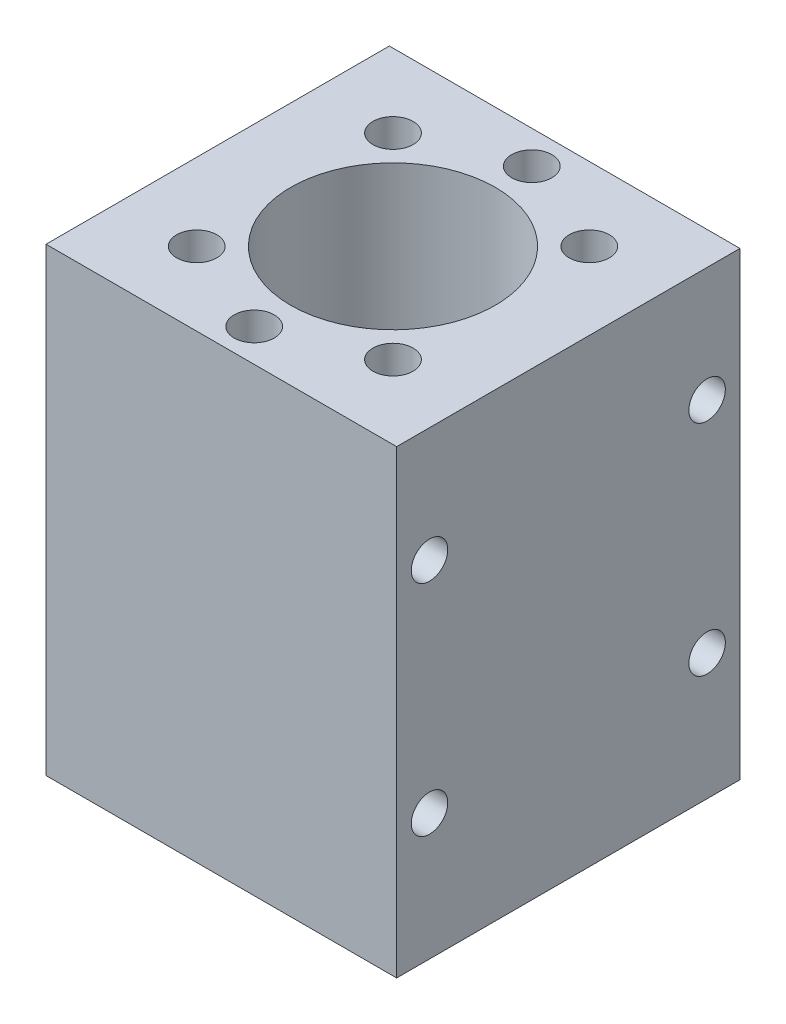
SolidWorks part; units mm, degrees
ref_plane "Спереди" through (0, 0, 0) normal (0, 0, 1) x (1, 0, 0)
ref_plane "Сверху" through (0, 0, 0) normal (0, 1, 0) x (1, 0, 0)
ref_plane "Справа" through (0, 0, 0) normal (1, 0, 0) x (0, 0, -1)
sketch "Эскиз1" plane through (0, 0, 0) normal (0, 1, 0) x (1, 0, 0)
  line L1 (-24, -23.5) -> (24, -23.5)
  line L2 (-24, -23.5) -> (-24, 23.5)
  line L3 (-24, 23.5) -> (24, 23.5)
  line L4 (24, -23.5) -> (24, 23.5)
  line L5 (-24, -23.5) -> (24, 23.5) construction
  line L6 (-24, 23.5) -> (24, -23.5) construction
  circle A0 centre (0, 0) radius 14
  dimension "D1" = 28
extrude "Бобышка-Вытянуть1" add sketch "Эскиз1" along normal blind 63
sketch "Эскиз2" plane through (-24, 0, 0) normal (-1, 0, 0) x (0, 0, 1)
  circle A0 centre (-19, 47.3) radius 2.5
  circle A1 centre (-19, 17.3) radius 2.5
  circle A2 centre (19, 47.3) radius 2.5
  circle A3 centre (19, 17.3) radius 2.5
extrude "Вырез-Вытянуть1" cut sketch "Эскиз2" against normal through all
sketch "Эскиз3" plane through (0, 63, 0) normal (0, 1, 0) x (1, 0, 0)
  circle A0 centre (13.435, -13.435) radius 2.75
  circle A1 centre (0, -19) radius 2.75
  circle A2 centre (-13.435, -13.435) radius 2.75
  circle A3 centre (13.435, 13.435) radius 2.75
  circle A4 centre (0, 19) radius 2.75
  circle A5 centre (-13.435, 13.435) radius 2.75
extrude "Вырез-Вытянуть2" cut sketch "Эскиз3" against normal blind 10
